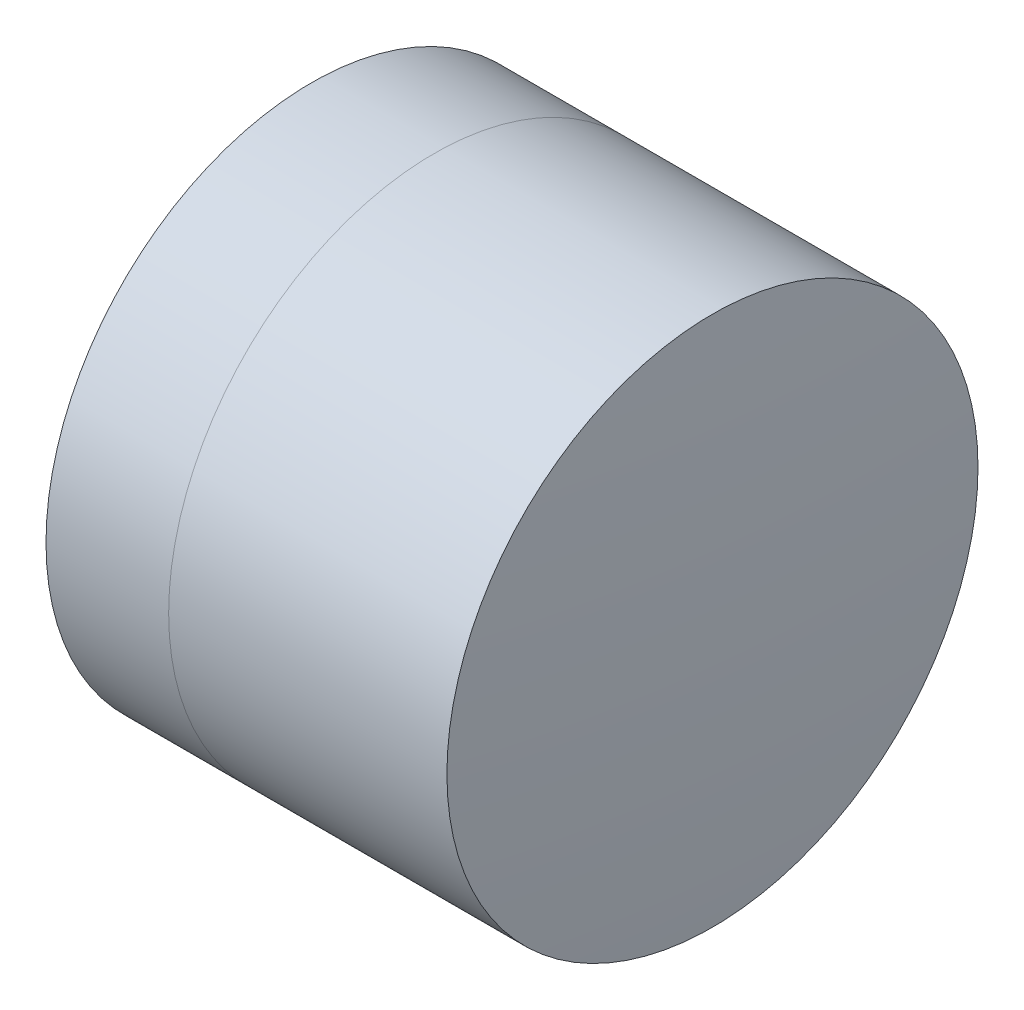
SolidWorks part; units mm, degrees
ref_plane "前视基准面" through (0, 0, 0) normal (0, 0, 1) x (1, 0, 0)
ref_plane "上视基准面" through (0, 0, 0) normal (0, 1, 0) x (1, 0, 0)
ref_plane "右视基准面" through (0, 0, 0) normal (1, 0, 0) x (0, 0, -1)
sketch "草图1" plane through (0, 0, 0) normal (0, 1, 0) x (1, 0, 0)
  line L0 (124.5233, 0) -> (646.9917, 0) construction
  line L1 (257.4708, -2.5) -> (258.6255, -2.5)
  line L2 (257.4708, 2.5) -> (258.6255, 2.5)
  arc A0 (258.6255, -2.5) -> (258.6255, 2.5) centre (255.6321, 0) ccw
  arc A1 (257.4708, 2.5) -> (257.4708, -2.5) centre (261.3321, 0) ccw
  point P10 (256.7321, 0)
  point P11 (259.5321, 0)
  dimension "D3" = 4.6
  dimension "D4" = 3.9
  dimension "D1" = 2.5
  dimension "D2" = 2.5
  dimension "D5" = 2.8
revolve "旋转1" add sketch "草图1" angle 360 about L0
sketch "草图2" plane through (0, 0, 0) normal (0, 1, 0) x (1, 0, 0)
  line L0 (-0.5519, 0) -> (622.6607, 0) construction
  line L2 (258.6255, 2.5) -> (261.2452, 2.5)
  line L3 (258.6255, -2.5) -> (261.2452, -2.5)
  arc A0 (261.2452, -2.5) -> (261.2452, 2.5) centre (225.3321, 0) ccw
  arc A1 (258.6255, -2.5) -> (258.6255, 2.5) centre (255.6321, 0) ccw construction
  arc A2 (258.6255, -2.5) -> (258.6255, 2.5) centre (255.6321, 0) ccw
  point P4 (259.5321, 0)
  point P8 (261.3321, 0)
  dimension "D1" = 36
  dimension "D2" = 1.8
revolve "旋转3" add sketch "草图2" angle 360 about L0
